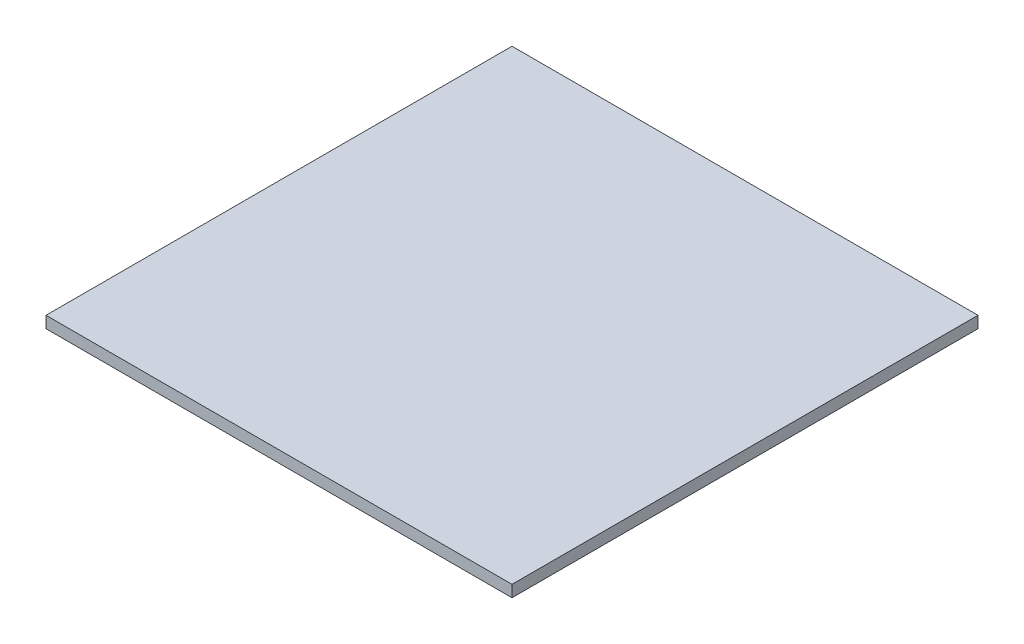
SolidWorks part; units mm, degrees
ref_plane "Front Plane" through (0, 0, 0) normal (0, 0, 1) x (1, 0, 0)
ref_plane "Top Plane" through (0, 0, 0) normal (0, 1, 0) x (1, 0, 0)
ref_plane "Right Plane" through (0, 0, 0) normal (1, 0, 0) x (0, 0, -1)
sketch "Sketch1" plane through (0, 0, 0) normal (0, 1, 0) x (1, 0, 0)
  line L1 (0, 0) -> (120, 0)
  line L2 (0, 0) -> (0, 120)
  line L3 (0, 120) -> (120, 120)
  line L4 (120, 0) -> (120, 120)
  dimension "D1" = 120
  dimension "D2" = 120
extrude "Boss-Extrude1" add sketch "Sketch1" along normal blind 3
